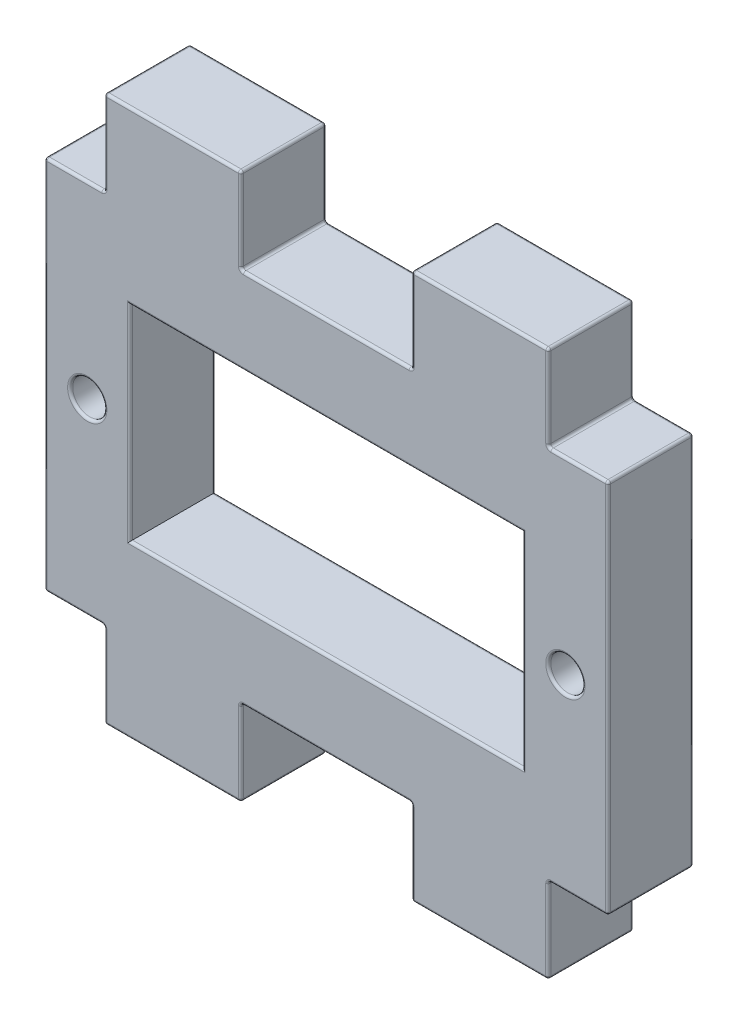
SolidWorks part; units mm, degrees
ref_plane "Ön Düzlem" through (0, 0, 0) normal (0, 0, 1) x (1, 0, 0)
ref_plane "Üst Düzlem" through (0, 0, 0) normal (0, 1, 0) x (1, 0, 0)
ref_plane "Sağ Düzlem" through (0, 0, 0) normal (1, 0, 0) x (0, 0, -1)
sketch "Sketch1" plane through (0, 0, 0) normal (0, 0, 1) x (1, 0, 0)
  line L0 (-16.5, 11) -> (16.5, 11)
  line L1 (-11.5, -6) -> (11.5, -6)
  line L2 (-11.5, -6) -> (-11.5, 6)
  line L3 (-11.5, 6) -> (11.5, 6)
  line L4 (11.5, -6) -> (11.5, 6)
  line L5 (-11.5, -6) -> (11.5, 6) construction
  line L6 (-11.5, 6) -> (11.5, -6) construction
  line L7 (16.5, -11) -> (16.5, 11)
  line L8 (-16.5, -11) -> (16.5, -11)
  line L9 (-16.5, -11) -> (-16.5, 11)
  line L10 (0, 6) -> (0, 0) construction
  line L11 (-13, 16) -> (-5, 16)
  line L12 (-13, 16) -> (-13, 11)
  line L13 (-13, 11) -> (-5, 11)
  line L14 (-5, 16) -> (-5, 11)
  line L15 (-13, 16) -> (-5, 11) construction
  line L16 (-13, 11) -> (-5, 16) construction
  line L17 (0, 0) -> (-11.5, 0) construction
  line L18 (5, 16) -> (5, 11)
  line L19 (13, 16) -> (5, 16)
  line L20 (13, 16) -> (13, 11)
  line L21 (13, -16) -> (13, -11)
  line L22 (13, -16) -> (5, -16)
  line L23 (5, -16) -> (5, -11)
  line L24 (-5, -16) -> (-5, -11)
  line L25 (-13, -16) -> (-5, -16)
  line L26 (-13, -16) -> (-13, -11)
  line L27 (-11.5, 0) -> (-16.5, 0) construction
  circle A0 centre (-14, 0) radius 1
  circle A1 centre (14, 0) radius 1
  point P0 (0, 0)
  point P10 (-9, 13.5)
  dimension "D7" = 2
  dimension "D1" = 12
  dimension "D2" = 23
  dimension "D4" = 3.5
  dimension "D5" = 5
  dimension "D6" = 8
  dimension "D8" = 2.5
  dimension "D3" = 5
extrude "Boss-Extrude1" add sketch "Sketch1" along normal mid plane 5 contours L26 L25 L24 L8 | L23 L22 L21 L8 | L9 L8 L7 L0 L4 L1 L2 L3 A0 A1 | L20 L19 L18 L0 | L11 L14 L13 L12
fillet "Fillet2" radius 0.15 60 edges at (-13, -16, 0) (-9, -16, -2.5) (-13, -13.5, -2.5) (-5, -16, 0) (-9, -16, 2.5) (-13, -13.5, 2.5) (-13, -11, 0) (-5, -13.5, -2.5) (-14.75, -11, -2.5) (-5, -11, 0) (-5, -13.5, 2.5) (-14.75, -11, 2.5) (-16.5, -11, 0) (0, -11, -2.5) (-16.5, 0, -2.5) (5, -11, 0) (0, -11, 2.5) (-16.5, 0, 2.5) (-16.5, 11, 0) (5, -13.5, -2.5) (-14.75, 11, -2.5) (5, -13.5, 2.5) (5, -16, 0) (-14.75, 11, 2.5) (-13, 11, 0) (9, -16, -2.5) (-13, 13.5, -2.5) (9, -16, 2.5) (13, -16, 0) (-13, 13.5, 2.5) (-13, 16, 0) (13, -13.5, -2.5) (-9, 16, -2.5) (13, -11, 0) (13, -13.5, 2.5) (-9, 16, 2.5) (-5, 16, 0) (14.75, -11, -2.5) (-5, 13.5, -2.5) (16.5, -11, 0) (14.75, -11, 2.5) (-5, 13.5, 2.5) (-5, 11, 0) (16.5, 0, -2.5) (0, 11, -2.5) (16.5, 11, 0) (16.5, 0, 2.5) (5, 11, 0) (0, 11, 2.5) (14.75, 11, -2.5) (5, 13.5, -2.5) (14.75, 11, 2.5) (13, 11, 0) (5, 13.5, 2.5) (5, 16, 0) (13, 13.5, -2.5) (9, 16, -2.5) (13, 13.5, 2.5) (9, 16, 2.5) (13, 16, 0)
fillet "Fillet3" radius 0.15 12 edges at (15, 0, 2.5) (-13, 0, 2.5) (0, 6, 2.5) (-11.5, 0, 2.5) (0, -6, 2.5) (11.5, 0, 2.5) (0, -6, -2.5) (-11.5, 0, -2.5) (0, 6, -2.5) (11.5, 0, -2.5) (-13, 0, -2.5) (15, 0, -2.5)
